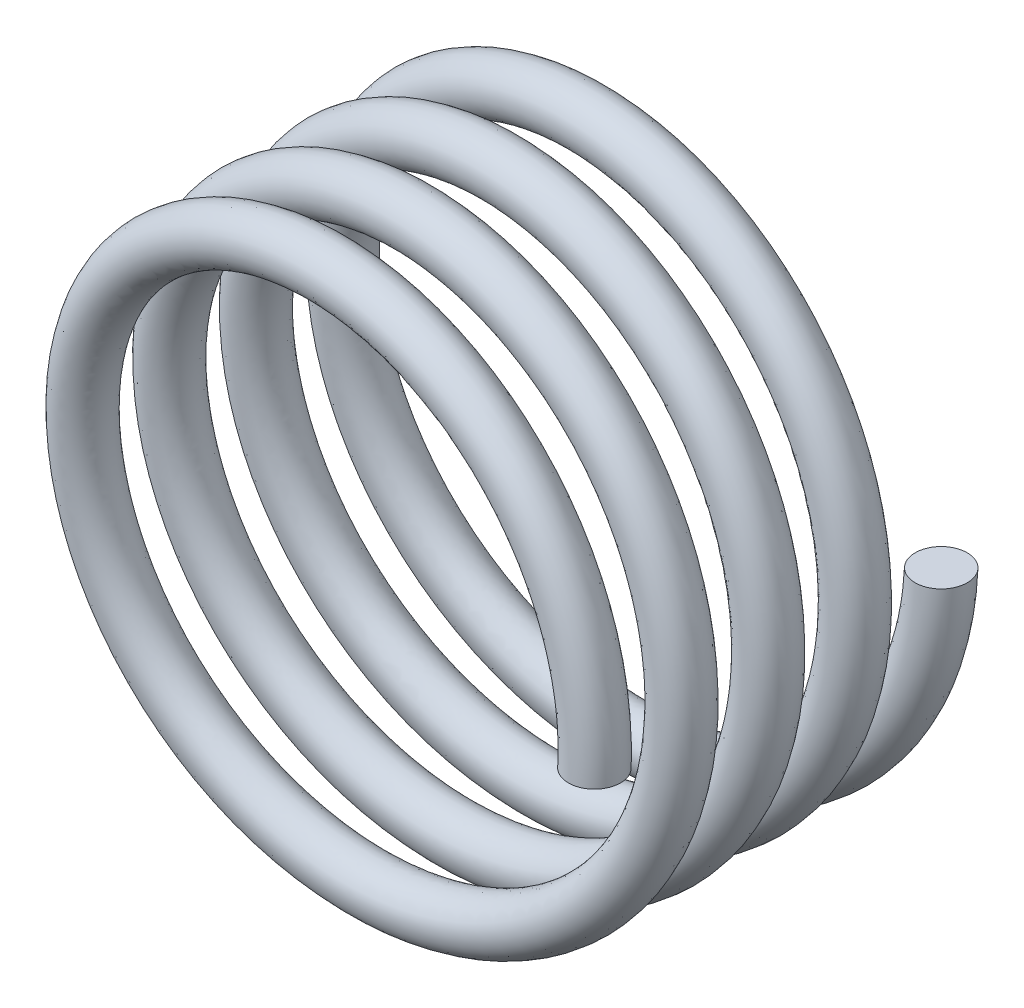
SolidWorks part; units mm, degrees
ref_plane "Alzado" through (0, 0, 0) normal (0, 0, 1) x (1, 0, 0)
ref_plane "Planta" through (0, 0, 0) normal (0, 1, 0) x (1, 0, 0)
ref_plane "Vista lateral" through (0, 0, 0) normal (1, 0, 0) x (0, 0, -1)
sketch "Croquis1" plane through (0, 0, 0) normal (0, 0, 1) x (1, 0, 0)
  circle A0 centre (0, 0) radius 80
  dimension "D1" = 160
curve "Hélice/Espiral1" pitch 25 height 100 turns 4
sketch "Croquis3" plane through (0, 0, 0) normal (0, 1, 0) x (1, 0, 0)
  circle A0 centre (80, 0) radius 7.5
  spline S0 degree 3 poles (80, 0) (80, -0.2107) (79.3238, -0.633) (76.3067, -1.2658) (71.3629, -1.8987) (64.6172, -2.5316) (56.24, -3.1646) (46.4428, -3.7975) (35.4729, -4.4304) (23.6074, -5.0633) (11.1457, -5.6962) (-1.5973, -6.3291) (-14.3, -6.962) (-26.6417, -7.5949) (-38.3106, -8.2278) (-49.0123, -8.8608) (-58.4764, -9.4937) (-66.464, -10.1266) (-72.7735, -10.7595) (-77.2455, -11.3924) (-79.767, -12.0253) (-80.2746, -12.6582) (-78.7552, -13.2911) (-75.2473, -13.9241) (-69.8395, -14.557) (-62.6683, -15.1899) (-53.9148, -15.8228) (-43.7999, -16.4557) (-32.5791, -17.0886) (-20.5357, -17.7215) (-7.9739, -18.3544) (4.7894, -18.9873) (17.4317, -19.6203) (29.6338, -20.2532) (41.0877, -20.8861) (51.5042, -21.519) (60.6203, -22.1519) (68.2057, -22.7848) (74.069, -23.4177) (78.062, -24.0506) (80.0841, -24.6835) (80.0841, -25.3165) (78.062, -25.9494) (74.069, -26.5823) (68.2057, -27.2152) (60.6203, -27.8481) (51.5042, -28.481) (41.0877, -29.1139) (29.6338, -29.7468) (17.4317, -30.3797) (4.7894, -31.0127) (-7.9739, -31.6456) (-20.5357, -32.2785) (-32.5791, -32.9114) (-43.7999, -33.5443) (-53.9148, -34.1772) (-62.6683, -34.8101) (-69.8395, -35.443) (-75.2473, -36.0759) (-78.7552, -36.7089) (-80.2746, -37.3418) (-79.767, -37.9747) (-77.2455, -38.6076) (-72.7735, -39.2405) (-66.464, -39.8734) (-58.4764, -40.5063) (-49.0123, -41.1392) (-38.3106, -41.7722) (-26.6417, -42.4051) (-14.3, -43.038) (-1.5973, -43.6709) (11.1457, -44.3038) (23.6074, -44.9367) (35.4729, -45.5696) (46.4428, -46.2025) (56.24, -46.8354) (64.6172, -47.4684) (71.3629, -48.1013) (76.3067, -48.7342) (79.3238, -49.3671) (80.3381, -50) (79.3238, -50.6329) (76.3067, -51.2658) (71.3629, -51.8987) (64.6172, -52.5316) (56.24, -53.1646) (46.4428, -53.7975) (35.4729, -54.4304) (23.6074, -55.0633) (11.1457, -55.6962) (-1.5973, -56.3291) (-14.3, -56.962) (-26.6417, -57.5949) (-38.3106, -58.2278) (-49.0123, -58.8608) (-58.4764, -59.4937) (-66.464, -60.1266) (-72.7735, -60.7595) (-77.2455, -61.3924) (-79.767, -62.0253) (-80.2746, -62.6582) (-78.7552, -63.2911) (-75.2473, -63.9241) (-69.8395, -64.557) (-62.6683, -65.1899) (-53.9148, -65.8228) (-43.7999, -66.4557) (-32.5791, -67.0886) (-20.5357, -67.7215) (-7.9739, -68.3544) (4.7894, -68.9873) (17.4317, -69.6203) (29.6338, -70.2532) (41.0877, -70.8861) (51.5042, -71.519) (60.6203, -72.1519) (68.2057, -72.7848) (74.069, -73.4177) (78.062, -74.0506) (80.0841, -74.6835) (80.0841, -75.3165) (78.062, -75.9494) (74.069, -76.5823) (68.2057, -77.2152) (60.6203, -77.8481) (51.5042, -78.481) (41.0877, -79.1139) (29.6338, -79.7468) (17.4317, -80.3797) (4.7894, -81.0127) (-7.9739, -81.6456) (-20.5357, -82.2785) (-32.5791, -82.9114) (-43.7999, -83.5443) (-53.9148, -84.1772) (-62.6683, -84.8101) (-69.8395, -85.443) (-75.2473, -86.0759) (-78.7552, -86.7089) (-80.2746, -87.3418) (-79.767, -87.9747) (-77.2455, -88.6076) (-72.7735, -89.2405) (-66.464, -89.8734) (-58.4764, -90.5063) (-49.0123, -91.1392) (-38.3106, -91.7722) (-26.6417, -92.4051) (-14.3, -93.038) (-1.5973, -93.6709) (11.1457, -94.3038) (23.6074, -94.9367) (35.4729, -95.5696) (46.4428, -96.2025) (56.24, -96.8354) (64.6172, -97.4684) (71.3629, -98.1013) (76.3067, -98.7342) (79.3238, -99.367) (80, -99.7893) (80, -100) knots 0 0 0 0 0.006329 0.012658 0.018987 0.025316 0.031646 0.037975 0.044304 0.050633 0.056962 0.063291 0.06962 0.075949 0.082278 0.088608 0.094937 0.101266 0.107595 0.113924 0.120253 0.126582 0.132911 0.139241 0.14557 0.151899 0.158228 0.164557 0.170886 0.177215 0.183544 0.189873 0.196203 0.202532 0.208861 0.21519 0.221519 0.227848 0.234177 0.240506 0.246835 0.253165 0.259494 0.265823 0.272152 0.278481 0.28481 0.291139 0.297468 0.303797 0.310127 0.316456 0.322785 0.329114 0.335443 0.341772 0.348101 0.35443 0.360759 0.367089 0.373418 0.379747 0.386076 0.392405 0.398734 0.405063 0.411392 0.417722 0.424051 0.43038 0.436709 0.443038 0.449367 0.455696 0.462025 0.468354 0.474684 0.481013 0.487342 0.493671 0.5 0.506329 0.512658 0.518987 0.525316 0.531646 0.537975 0.544304 0.550633 0.556962 0.563291 0.56962 0.575949 0.582278 0.588608 0.594937 0.601266 0.607595 0.613924 0.620253 0.626582 0.632911 0.639241 0.64557 0.651899 0.658228 0.664557 0.670886 0.677215 0.683544 0.689873 0.696203 0.702532 0.708861 0.71519 0.721519 0.727848 0.734177 0.740506 0.746835 0.753165 0.759494 0.765823 0.772152 0.778481 0.78481 0.791139 0.797468 0.803797 0.810127 0.816456 0.822785 0.829114 0.835443 0.841772 0.848101 0.85443 0.860759 0.867089 0.873418 0.879747 0.886076 0.892405 0.898734 0.905063 0.911392 0.917722 0.924051 0.93038 0.936709 0.943038 0.949367 0.955696 0.962025 0.968354 0.974684 0.981013 0.987342 0.993671 1 1 1 1 construction
  dimension "D1" = 15
sweep "Barrer7" add profiles "Croquis3" path "Hélice/Espiral1"
